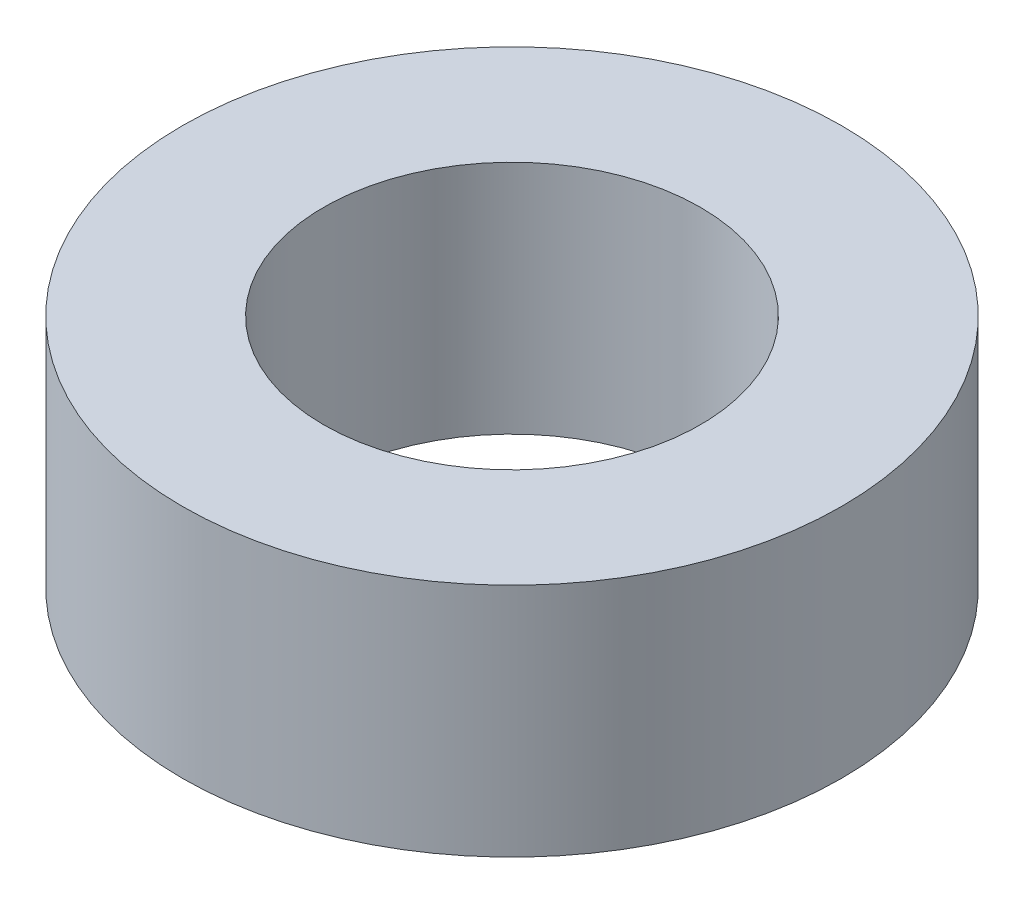
SolidWorks part; units mm, degrees
material "Plain Carbon Steel"
ref_plane "Front Plane" through (0, 0, 0) normal (0, 0, 1) x (1, 0, 0)
ref_plane "Top Plane" through (0, 0, 0) normal (0, 1, 0) x (1, 0, 0)
ref_plane "Right Plane" through (0, 0, 0) normal (1, 0, 0) x (0, 0, -1)
sketch "Sketch1" plane through (0, 0, 0) normal (0, 1, 0) x (1, 0, 0)
  circle A0 centre (0, 0) radius 3.5
  circle A1 centre (0, 0) radius 2
  dimension "D1" = 7
  dimension "D2" = 4
extrude "Boss-Extrude1" add sketch "Sketch1" along normal blind 2.5 contours A1 | A0
